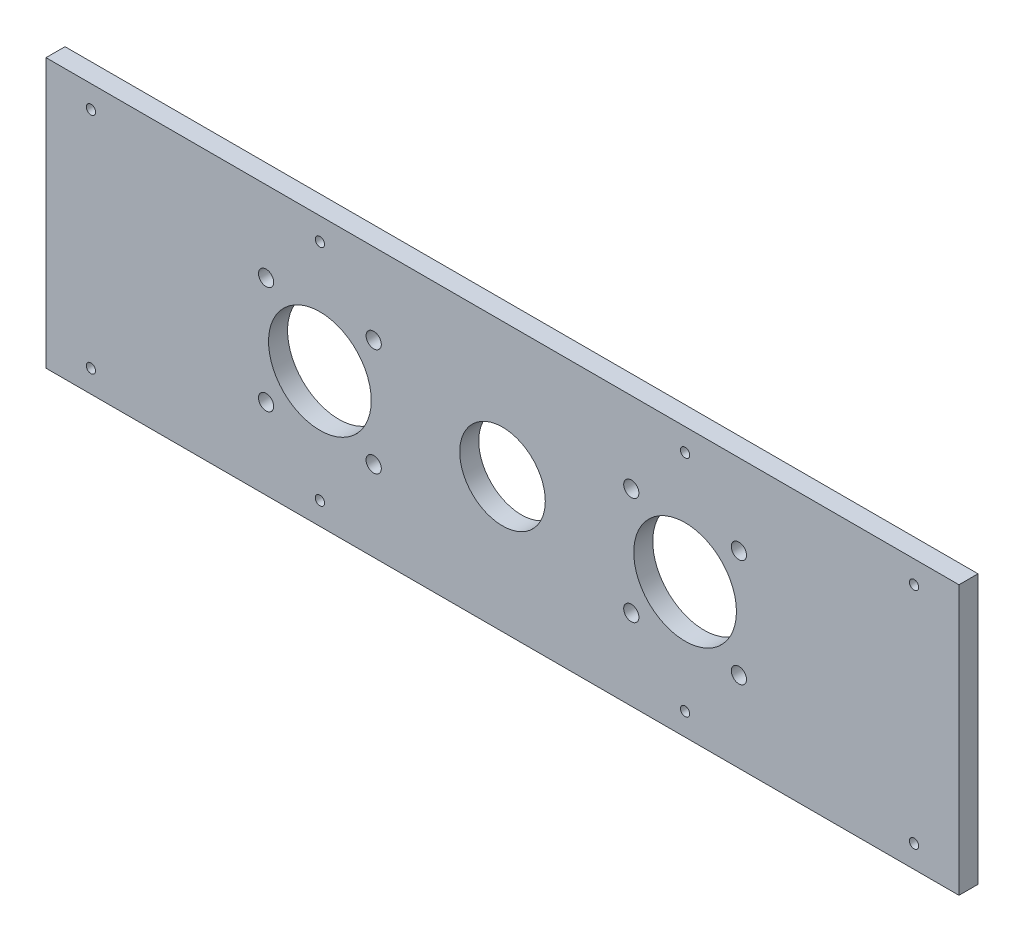
SolidWorks part; units mm, degrees
ref_plane "Front Plane" through (0, 0, 0) normal (0, 0, 1) x (1, 0, 0)
ref_plane "Top Plane" through (0, 0, 0) normal (0, 1, 0) x (1, 0, 0)
ref_plane "Right Plane" through (0, 0, 0) normal (1, 0, 0) x (0, 0, -1)
sketch "Sketch1" plane through (0, 0, 0) normal (0, 0, 1) x (1, 0, 0)
  line L1 (0, 0) -> (304.8, 0)
  line L2 (0, 0) -> (0, 89.8)
  line L3 (0, 89.8) -> (304.8, 89.8)
  line L4 (304.8, 0) -> (304.8, 89.8)
  circle A3 centre (152.4, 44.9) radius 14.2875
  point P7 (152.4, 44.9)
  circle B0 centre (109.4016, 62.8594) radius 2.54
  circle B1 centre (109.3994, 26.9384) radius 2.54
  circle B2 centre (73.4784, 26.9406) radius 2.54
  circle B3 centre (73.4806, 62.8616) radius 2.54
  circle B4 centre (91.44, 44.9) radius 17.145
  circle B5 centre (195.4006, 62.8616) radius 2.54
  circle B6 centre (231.3216, 62.8594) radius 2.54
  circle B7 centre (231.3194, 26.9384) radius 2.54
  circle B8 centre (195.3984, 26.9406) radius 2.54
  circle B9 centre (213.36, 44.9) radius 17.145
  dimension "D3" = 60.96
  dimension "D4" = 60.96
  dimension "D6" = 28.575
  dimension "D1" = 89.8
  dimension "D2" = 304.8
sketch_block_instance "Block1-1"
sketch_block "Block1" parameters "D1"=5.08, "D2"=34.29
sketch_block_instance "Block2-1"
sketch_block "Block2" parameters "D1"=5.08, "D2"=34.29
extrude "Boss-Extrude1" add sketch "Sketch1" along normal blind 6.35
sketch "Sketch2" plane through (0, 0, 0) normal (0, 0, -1) x (-1, 0, 0)
  line L0 (-304.8, 89.8) -> (0, 89.8) construction
  line L1 (-304.8, 0) -> (-304.8, 89.8) construction
  line L2 (-152.4, 89.8) -> (-152.4, 72.2833) construction
  line L3 (-304.8, 44.9) -> (-279.6853, 44.9) construction
  line L4 (0, 44.9) -> (-25.1147, 44.9) construction
  circle A0 centre (-289.8, 82.3) radius 1.55
  circle A1 centre (-213.36, 82.3) radius 1.55
  circle A2 centre (-91.44, 82.3) radius 1.55
  circle A3 centre (-15, 82.3) radius 1.55
  circle A4 centre (-15, 7.5) radius 1.55
  circle A5 centre (-91.44, 7.5) radius 1.55
  circle A6 centre (-213.36, 7.5) radius 1.55
  circle A7 centre (-289.8, 7.5) radius 1.55
  dimension "D1" = 3.1
  dimension "D4" = 3.1
  dimension "D2" = 7.5
  dimension "D3" = 15
extrude "Cut-Extrude1" cut sketch "Sketch2" against normal blind 10
